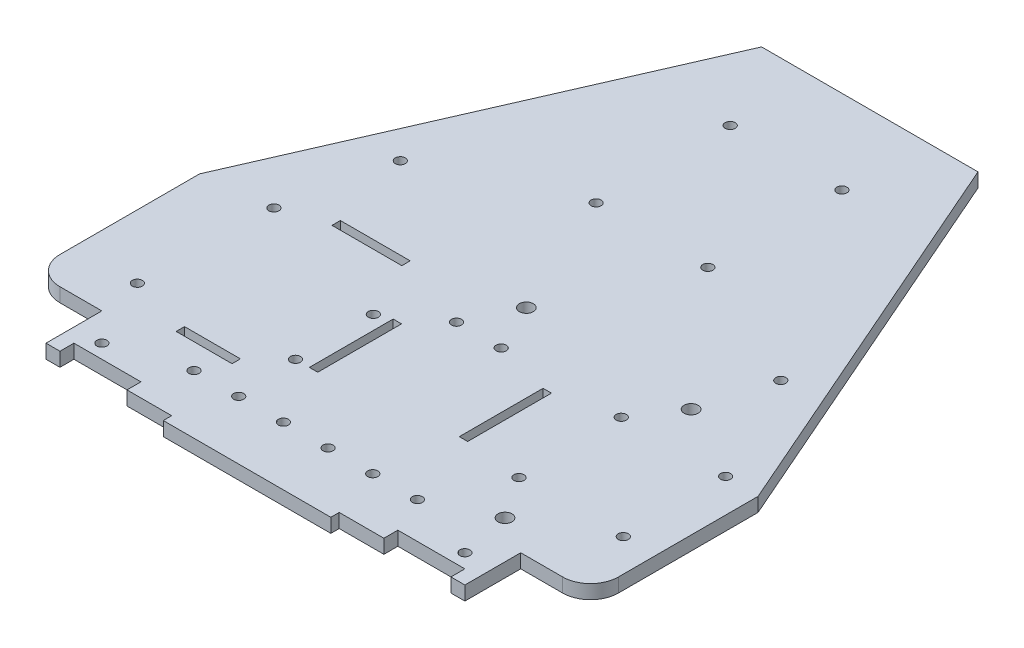
SolidWorks part; units mm, degrees
ref_plane "Front Plane" through (0, 0, 0) normal (0, 0, 1) x (1, 0, 0)
ref_plane "Top Plane" through (0, 0, 0) normal (0, 1, 0) x (1, 0, 0)
ref_plane "Right Plane" through (0, 0, 0) normal (1, 0, 0) x (0, 0, -1)
sketch "Sketch1" plane through (0, 0, 0) normal (0, 1, 0) x (1, 0, 0)
  line L8 (100, -40) -> (100, 10)
  line L10 (-30, 170) -> (30, 170)
  line L11 (30, 170) -> (100, 10)
  line L12 (-30, 170) -> (-100, 10)
  line L13 (-100, -40) -> (-100, 10)
  line L18 (75, -50) -> (90, -50)
  line L19 (-75, -70) -> (-75, -50)
  line L20 (-75, -50) -> (-90, -50)
  line L31 (-75, -70) -> (-30, -70)
  line L32 (75, -50) -> (75, -70)
  line L34 (30, -70) -> (75, -70)
  line L36 (30, -70) -> (30, -73)
  line L37 (30, -73) -> (-30, -73)
  line L38 (-30, -70) -> (-30, -73)
  arc A6 (90, -50) -> (100, -40) centre (90, -40) ccw
  arc A7 (-90, -50) -> (-100, -40) centre (-90, -40) cw
  point P9 (-75, -70)
  point P16 (75, -70)
  point P24 (-100, -70)
  dimension "D6" = 3
  dimension "D3" = 20
  dimension "D1" = 60
  dimension "D2" = 200
  dimension "D4" = 150
  dimension "D7" = 60
  dimension "D9" = 70
  dimension "D12" = 160
extrude "Boss-Extrude1" add sketch "Sketch1" along normal blind 5
sketch "Sketch3" plane through (0, 5, 0) normal (0, 1, 0) x (1, 0, 0)
  line L0 (-25.321, -35.0624) -> (-25.321, -40.0624) construction
  line L1 (-25.321, -40.0624) -> (-35.321, -40.0624) construction
  line L2 (-25.321, 12.7376) -> (-25.321, 17.7376) construction
  line L11 (-25.321, 17.7376) -> (-35.321, 17.7376) construction
  line L12 (-76.121, 12.7376) -> (-25.321, 12.7376) construction
  line L13 (-25.321, 12.7376) -> (-25.321, -2.4624) construction
  line L14 (-25.321, -2.4624) -> (-25.321, -30.3624) construction
  line L15 (-25.321, -30.3624) -> (-25.321, -35.0624) construction
  line L16 (-25.321, -35.0624) -> (-77.221, -35.0624) construction
  line L17 (-77.221, -35.0624) -> (-76.121, -35.0624) construction
  line L18 (-76.121, -35.0624) -> (-76.121, 12.7376) construction
  line L19 (-25.321, -30.3624) -> (-20.321, -30.3624) construction
  line L20 (-35.321, -40.0624) -> (-55.321, -40.0624)
  line L21 (-35.321, -40.0624) -> (-35.321, -43.0624)
  line L22 (-35.321, -43.0624) -> (-55.321, -43.0624)
  line L23 (-55.321, -40.0624) -> (-55.321, -43.0624)
  line L24 (-35.321, 17.7376) -> (-60.321, 17.7376)
  line L25 (-35.321, 17.7376) -> (-35.321, 20.7376)
  line L26 (-35.321, 20.7376) -> (-60.321, 20.7376)
  line L27 (-60.321, 17.7376) -> (-60.321, 20.7376)
  line L29 (-20.321, -30.3624) -> (-17.321, -30.3624)
  line L30 (-20.321, -30.3624) -> (-20.321, -0.3624)
  line L31 (-20.321, -0.3624) -> (-17.321, -0.3624)
  line L32 (-17.321, -30.3624) -> (-17.321, -0.3624)
  circle A4 centre (-76.121, 12.7376) radius 1.8
  circle A5 centre (-77.221, -35.0624) radius 1.8
  circle A6 centre (-25.321, -2.4624) radius 1.8
  circle A7 centre (-25.321, -30.3624) radius 1.8
  dimension "D8" = 10
  dimension "D9" = 3
  dimension "D10" = 10
  dimension "D11" = 20
  dimension "D21" = 3.6
  dimension "D22" = 3.6
  dimension "D23" = 3.6
  dimension "D24" = 3.6
  dimension "D3" = 27.9
  dimension "D4" = 15.2
  dimension "D5" = 4.7
  dimension "D6" = 5
  dimension "D7" = 5
  dimension "D12" = 3
  dimension "D13" = 25
  dimension "D14" = 5
  dimension "D15" = 50.8
  dimension "D16" = 30
  dimension "D17" = 3
  dimension "D19" = 51.9
  dimension "D20" = 1.1
extrude "arduino" cut sketch "Sketch3" against normal through all
sketch "Sketch6" plane through (0, 5, 0) normal (0, 1, 0) x (1, 0, 0)
  line L0 (0, 170) -> (0, 120) construction
  line L1 (30, 170) -> (-30, 170) construction
  line L7 (0, 120) -> (20, 120) construction
  circle A4 centre (20, 120) radius 1.8
  circle A5 centre (-20, 120) radius 1.8
  dimension "D3" = 3.6
  dimension "D1" = 50
  dimension "D2" = 20
extrude "Cut-Extrude4" cut sketch "Sketch6" against normal through all
sketch "Sketch8" plane through (0, 5, 0) normal (0, 1, 0) x (1, 0, 0)
  line L0 (-75, -50) -> (-75, -60) construction
  line L1 (0, -73) -> (0, -52) construction
  line L2 (8, -52) -> (24, -52) construction
  line L3 (30, 170) -> (-30, 170) construction
  line L4 (-75, -50) -> (-75, -70) construction
  line L5 (-100, 10) -> (100, 10) construction
  line L6 (0, 170) -> (0, 38.0278) construction
  line L7 (0, 10) -> (8, 10) construction
  line L8 (-75, -60) -> (-65, -60) construction
  line L9 (0, -55) -> (0, 55) construction
  line L10 (24, -52) -> (40, -52) construction
  line L11 (-30, -73) -> (30, -73) construction
  line L13 (0, -52) -> (8, -52) construction
  circle A16 centre (8, 10) radius 1.8
  circle A17 centre (-8, 10) radius 1.8
  circle A18 centre (-65, -60) radius 1.8
  circle A19 centre (65, -60) radius 1.8
  circle A28 centre (8, -52) radius 1.8
  circle A33 centre (24, -52) radius 1.8
  circle A34 centre (40, -52) radius 1.8
  circle A35 centre (-8, -52) radius 1.8
  circle A36 centre (-40, -52) radius 1.8
  circle A37 centre (-24, -52) radius 1.8
  dimension "D6" = 8
  dimension "D7" = 3.6
  dimension "D8" = 3.6
  dimension "D9" = 16
  dimension "D2" = 10
  dimension "D11" = 3.6
  dimension "D5" = 8
  dimension "D3" = 3.6
  dimension "D12" = 3.6
  dimension "D1" = 10
  dimension "D4" = 21
  dimension "D10" = 16
extrude "Cut-Extrude5" cut sketch "Sketch8" against normal blind 10
sketch "Sketch9" plane through (0, 5, 0) normal (0, 1, 0) x (1, 0, 0)
  line L0 (0, 72) -> (20, 72) construction
  line L1 (87.9982, 10.3676) -> (88.3658, -26.6306) construction
  line L2 (51.3676, -26.9982) -> (88.3658, -26.6306) construction
  line L4 (-100, 10) -> (-100, 60) construction
  line L5 (-100, 60) -> (-68.125, 60) construction
  line L6 (0, 72) -> (-20, 72) construction
  line L10 (51, 10) -> (51.3676, -26.9982) construction
  line L11 (51, 10) -> (87.9982, 10.3676) construction
  line L12 (-68.125, 60) -> (-68.125, 50) construction
  line L13 (0, -2.75) -> (0, 2.75) construction
  line L14 (51, 10) -> (51, 25) construction
  line L15 (51, 25) -> (61, 25) construction
  line L16 (51.3676, -26.9982) -> (51.3676, -41.9982) construction
  line L17 (51.3676, -41.9982) -> (61.3676, -41.9982) construction
  line L18 (51, 10) -> (31, 10) construction
  line L19 (31, 10) -> (31, 5) construction
  line L20 (0, 72) -> (0, 27) construction
  line L34 (31, 5) -> (28, 5)
  line L35 (31, 5) -> (31, -25)
  line L36 (31, -25) -> (28, -25)
  line L37 (28, 5) -> (28, -25)
  circle A12 centre (20, 72) radius 1.8
  circle A13 centre (-20, 72) radius 1.8
  circle A14 centre (51, 10) radius 1.8
  circle A15 centre (87.9982, 10.3676) radius 1.8
  circle A16 centre (88.3658, -26.6306) radius 1.8
  circle A17 centre (51.3676, -26.9982) radius 1.8
  circle A18 centre (-68.125, 50) radius 1.8
  circle A19 centre (68.125, 50) radius 1.8
  circle A20 centre (61, 25) radius 2.5
  circle A21 centre (61.3676, -41.9982) radius 2.5
  circle A22 centre (0, 27) radius 2.5
  dimension "D3" = 3.6
  dimension "D4" = 3.6
  dimension "D5" = 50
  dimension "D7" = 3.6
  dimension "D8" = 3.6
  dimension "D9" = 3.6
  dimension "D10" = 3.6
  dimension "D12" = 10
  dimension "D13" = 3.6
  dimension "D16" = 5
  dimension "D19" = 5
  dimension "D24" = 5
  dimension "D1" = 20
  dimension "D2" = 20
  dimension "D6" = 31.875
  dimension "D11" = 37
  dimension "D14" = 15
  dimension "D15" = 10
  dimension "D17" = 15
  dimension "D18" = 10
  dimension "D20" = 20
  dimension "D21" = 5
  dimension "D22" = 30
  dimension "D23" = 45
  dimension "D25" = 3
extrude "l298n" cut sketch "Sketch9" against normal blind 10
ref_point "bottomofcart"
sketch "Sketch11" plane through (0, 5, 0) normal (0, 1, 0) x (1, 0, 0)
  line L0 (-75, -70) -> (-70, -70) construction
  line L1 (-75, -70) -> (-30, -70) construction
  line L2 (0, -2.75) -> (0, 2.75) construction
  line L3 (-70, -70) -> (-46, -70)
  line L4 (-70, -70) -> (-70, -65)
  line L5 (-70, -65) -> (-46, -65)
  line L6 (-46, -70) -> (-46, -65)
  line L7 (46, -70) -> (46, -65)
  line L8 (70, -70) -> (70, -65)
  line L9 (70, -65) -> (46, -65)
  line L10 (70, -70) -> (46, -70)
  dimension "D1" = 5
  dimension "D2" = 5
  dimension "D3" = 24
extrude "Cut-Extrude7" cut sketch "Sketch11" against normal blind 10
sketch "Sketch12" plane through (0, 5, 0) normal (0, 1, 0) x (1, 0, 0)
  line L0 (30, 170) -> (50, 170) construction
  line L2 (50, 170) -> (-50, 170)
  line L3 (50, 170) -> (50, 150)
  line L4 (50, 150) -> (-50, 150)
  line L5 (-50, 170) -> (-50, 150)
  dimension "D1" = 20
  dimension "D2" = 20
  dimension "D3" = 100
extrude "Cut-Extrude8" cut sketch "Sketch12" against normal blind 10
